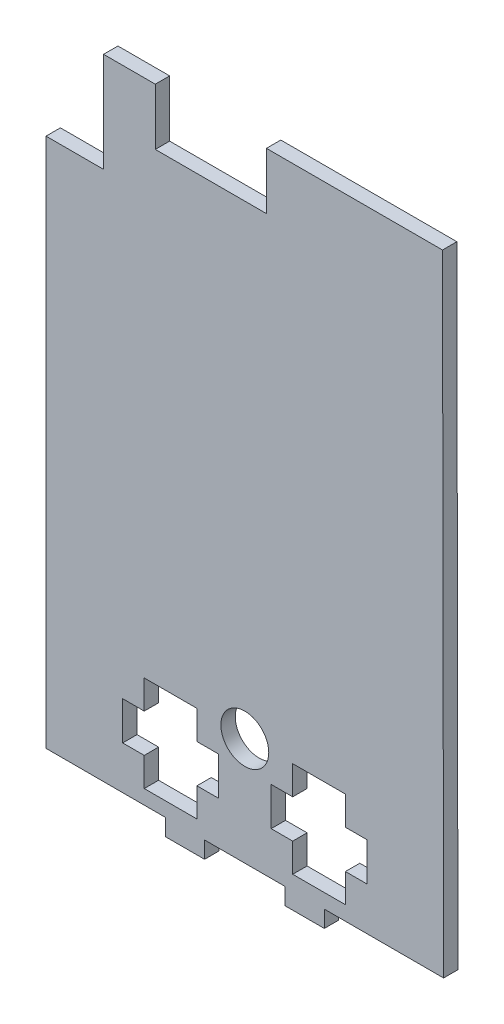
SolidWorks part; units mm, degrees
ref_plane "Alzado" through (0, 0, 0) normal (0, 0, 1) x (1, 0, 0)
ref_plane "Planta" through (0, 0, 0) normal (0, 1, 0) x (1, 0, 0)
ref_plane "Vista lateral" through (0, 0, 0) normal (1, 0, 0) x (0, 0, -1)
sketch "Model" plane through (0, 0, 0) normal (0, 0, 1) x (1, 0, 0)
  line L0 (112.5018, 58.3262) -> (112.5018, 36.5036)
  line L1 (112.5018, 36.5036) -> (112.5018, 1.8191)
  line L2 (112.5018, 1.8191) -> (112.5018, -9.0033)
  line L3 (195.5018, -52.3929) -> (195.2754, 79.1244)
  line L4 (170.6018, -52.3853) -> (195.5018, -52.3929)
  line L5 (170.6018, -55.8853) -> (170.6018, -52.3853)
  line L6 (162.4018, -55.8853) -> (170.6018, -55.8853)
  line L7 (162.4018, -52.3853) -> (162.4018, -55.8853)
  line L8 (145.6018, -52.3853) -> (162.4018, -52.3853)
  line L9 (145.6018, -55.8853) -> (145.6018, -52.3853)
  line L10 (137.4018, -55.8853) -> (145.6018, -55.8853)
  line L11 (137.4018, -52.3917) -> (137.4018, -55.8853)
  line L12 (112.5018, -52.3776) -> (137.4018, -52.3917)
  line L13 (112.5018, -9.0033) -> (112.5018, -52.3776)
  line L14 (124.5112, 58.3173) -> (112.5018, 58.3262)
  line L15 (195.2754, 79.1244) -> (158.4942, 79.1244)
  line L16 (158.5107, 67.3251) -> (158.5107, 79.1244)
  line L17 (158.5107, 67.3251) -> (135.3107, 67.3264)
  line L18 (135.3107, 79.1244) -> (135.3107, 67.3244)
  line L19 (124.5112, 79.1244) -> (124.5112, 58.3152)
  line L20 (144.0018, -49.3895) -> (144.0018, -43.3895)
  line L21 (175.0018, -49.3896) -> (175.0018, -43.3896)
  line L22 (133.0018, -49.3895) -> (144.0018, -49.3895)
  line L23 (164.0018, -49.3896) -> (175.0018, -49.3896)
  line L24 (133.0018, -43.3895) -> (133.0018, -49.3895)
  line L25 (164.0018, -43.3896) -> (164.0018, -49.3896)
  line L26 (148.5018, -43.3895) -> (144.0018, -43.3895)
  line L27 (179.5018, -43.3896) -> (175.0018, -43.3896)
  line L28 (148.5018, -35.3895) -> (148.5018, -43.3895)
  line L29 (179.5018, -35.3896) -> (179.5018, -43.3896)
  line L30 (144.0018, -35.3895) -> (148.5018, -35.3895)
  line L31 (175.0018, -35.3896) -> (179.5018, -35.3896)
  line L32 (144.0018, -29.3895) -> (144.0018, -35.3895)
  line L33 (175.0018, -29.3896) -> (175.0018, -35.3896)
  line L34 (133.0018, -29.3895) -> (144.0018, -29.3895)
  line L35 (164.0018, -29.3896) -> (175.0018, -29.3896)
  line L36 (133.0018, -35.3895) -> (133.0018, -29.3895)
  line L37 (164.0018, -35.3896) -> (164.0018, -29.3896)
  line L38 (128.5018, -35.3895) -> (133.0018, -35.3895)
  line L39 (159.5018, -35.3896) -> (164.0018, -35.3896)
  line L40 (128.5018, -43.3895) -> (128.5018, -35.3895)
  line L41 (159.5018, -43.3896) -> (159.5018, -35.3896)
  line L42 (133.0018, -43.3895) -> (128.5018, -43.3895)
  line L43 (164.0018, -43.3896) -> (159.5018, -43.3896)
  line L44 (135.3107, 79.1244) -> (124.5112, 79.1244)
  circle A0 centre (154.0018, -29.8853) radius 5
extrude "Saliente-Extruir1" add sketch "Model" along normal blind 3
